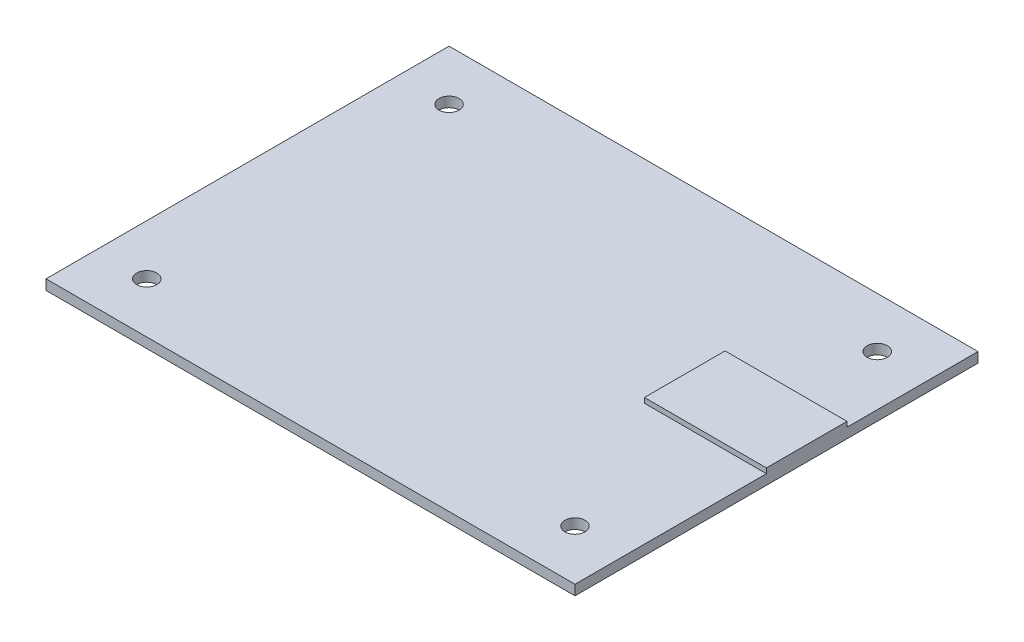
SolidWorks part; units mm, degrees
ref_plane "Alzado" through (0, 0, 0) normal (0, 0, 1) x (1, 0, 0)
ref_plane "Planta" through (0, 0, 0) normal (0, 1, 0) x (1, 0, 0)
ref_plane "Vista lateral" through (0, 0, 0) normal (1, 0, 0) x (0, 0, -1)
sketch "Croquis1" plane through (0, 0, 0) normal (0, 1, 0) x (1, 0, 0)
  line L0 (-42.5, 30) -> (42.5, 30) construction
  line L1 (-52.5, 40) -> (52.5, 40)
  line L2 (-52.5, 40) -> (-52.5, -40)
  line L3 (-52.5, -40) -> (52.5, -40)
  line L4 (52.5, 40) -> (52.5, -40)
  line L5 (-52.5, 40) -> (52.5, -40) construction
  line L6 (-52.5, -40) -> (52.5, 40) construction
  line L7 (42.5, 30) -> (42.5, -30) construction
  line L8 (-42.5, -30) -> (42.5, -30) construction
  line L9 (-42.5, 30) -> (-42.5, -30) construction
  line L10 (0, 0) -> (0, 30) construction
  circle A0 centre (-42.5, 30) radius 2
  circle A1 centre (-42.5, -30) radius 2
  circle A4 centre (42.5, -30) radius 2
  circle A5 centre (42.5, 30) radius 2
  point P0 (0, 0)
  dimension "D4" = 4
  dimension "D5" = 4
  dimension "D1" = 105
  dimension "D2" = 80
  dimension "D3" = 10
extrude "Saliente-Extruir1" add sketch "Croquis1" along normal blind 2
sketch "Croquis2" plane through (0, 0, 0) normal (0, 1, 0) x (1, 0, 0)
  line L0 (52.5, -40) -> (52.5, 40) construction
  line L1 (52.5, -2) -> (28.287, -2)
  line L2 (52.5, -2) -> (52.5, 14)
  line L3 (52.5, 14) -> (28.287, 14)
  line L4 (28.287, -2) -> (28.287, 14)
  line L5 (-52.5, -40) -> (52.5, -40) construction
  dimension "D1" = 38
  dimension "D2" = 54
extrude "Saliente-Extruir2" add sketch "Croquis2" along normal blind 3
